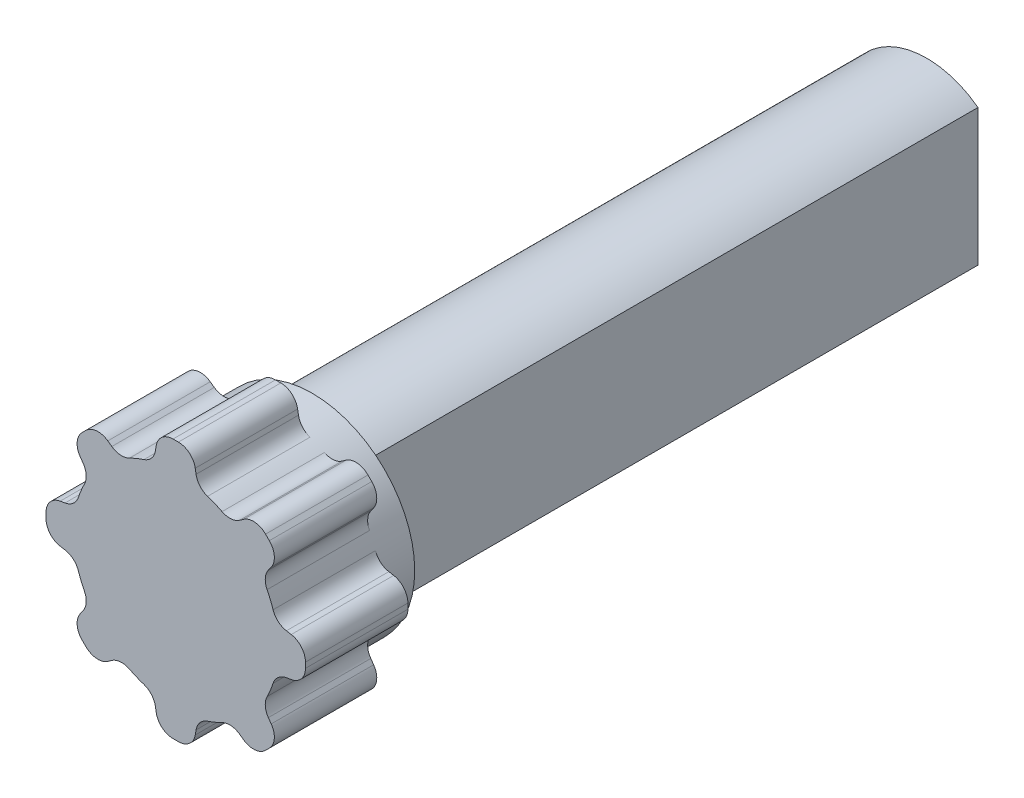
SolidWorks part; units mm, degrees
ref_plane "Front Plane" through (0, 0, 0) normal (0, 0, 1) x (1, 0, 0)
ref_plane "Top Plane" through (0, 0, 0) normal (0, 1, 0) x (1, 0, 0)
ref_plane "Right Plane" through (0, 0, 0) normal (1, 0, 0) x (0, 0, -1)
sketch "Sketch1" plane through (0, 0, 0) normal (0, 0, 1) x (1, 0, 0)
  line L0 (1.905, 2.54) -> (1.905, -2.54)
  arc A0 (1.905, 2.54) -> (1.905, -2.54) centre (0, 0) ccw
  dimension "D1" = 6.35
  dimension "D2" = 5.08
extrude "Boss-Extrude1" add sketch "Sketch1" against normal blind 25.4
sketch "Sketch2" plane through (0, 0, 0) normal (0, 0, 1) x (1, 0, 0)
  circle A1 centre (0, 0) radius 3.81
  dimension "D1" = 7.62
extrude "Boss-Extrude2" add sketch "Sketch2" along normal mid plane 5.08
sketch "Sketch4" plane through (0, 0, 2.54) normal (0, 0, 1) x (1, 0, 0)
  line L0 (0, 0) -> (0, 3.81) construction
  line L3 (0, 3.81) -> (0, 4.826) construction
  line L4 (-0.635, 4.826) -> (0.635, 4.826)
  line L5 (-0.635, 4.826) -> (-0.8246, 3.7197)
  line L6 (-0.8246, 3.7197) -> (0.8246, 3.7197)
  line L7 (0.8246, 3.7197) -> (0.635, 4.826)
  line L8 (-0.8246, 3.7197) -> (0, 0) construction
  line L9 (0, 0) -> (0.8246, 3.7197) construction
  circle A2 centre (0, 0) radius 3.81 construction
  point P12 (0, 4.826)
  dimension "D1" = 1.27
  dimension "D2" = 1.016
  dimension "D3" = 25
extrude "Boss-Extrude3" add sketch "Sketch4" against normal offset from surface (3.81 mm away) 1.27 up to face at (-0.635, 0, -2.54)
fillet "Fillet1" radius 0.635 4 edges at (-0.8246, 3.7197, 0.635) (-0.635, 4.826, 0.635) (0.8246, 3.7197, 0.635) (0.635, 4.826, 0.635)
pattern_circular "CirPattern1" count 8 over 360 about axis through (0, 0, 0) along (0, 0, 1) of "Boss-Extrude3", "Fillet1"
